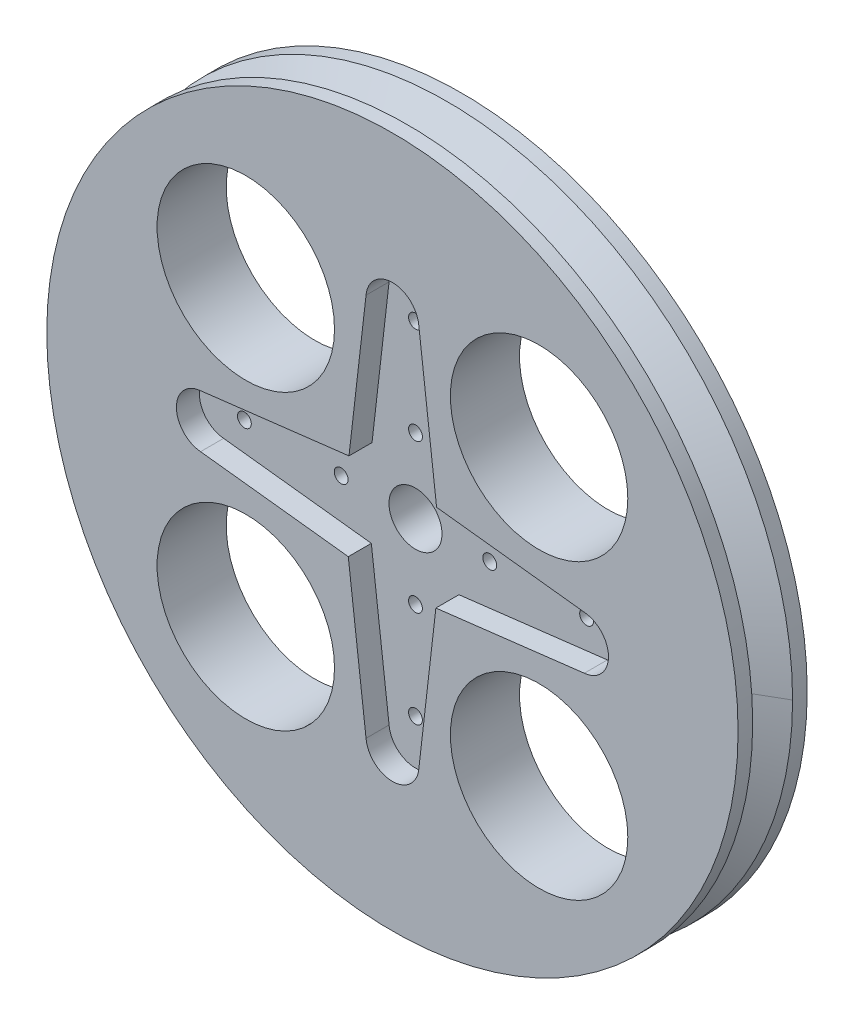
SolidWorks part; units mm, degrees
material "ABS"
ref_plane "Front Plane" through (0, 0, 0) normal (0, 0, 1) x (1, 0, 0)
ref_plane "Top Plane" through (0, 0, 0) normal (0, 1, 0) x (1, 0, 0)
ref_plane "Right Plane" through (0, 0, 0) normal (1, 0, 0) x (0, 0, -1)
sketch "Sketch1" plane through (0, 0, 0) normal (0, 0, 1) x (1, 0, 0)
  line L0 (-16.85, 0) -> (14.45, 0) construction
  line L1 (0, -6.45) -> (0, 6.45) construction
  line L2 (0, 0) -> (-21.2132, 21.2132) construction
  circle A0 centre (0, 0) radius 30
  circle A1 centre (-12.7279, 12.7279) radius 7.7
  circle A2 centre (12.7279, 12.7279) radius 7.7
  circle A3 centre (12.7279, -12.7279) radius 7.7
  circle A4 centre (-12.7279, -12.7279) radius 7.7
  circle A5 centre (0, 0) radius 2.3 construction
  circle A6 centre (0, 0) radius 2.3
  circle A7 centre (-14.85, 0) radius 0.6 construction
  circle A8 centre (-14.85, 0) radius 0.6
  circle A10 centre (6.45, 0) radius 0.6 construction
  circle A11 centre (6.45, 0) radius 0.6
  circle A12 centre (0, -6.45) radius 0.6
  circle A13 centre (-6.45, 0) radius 0.6
  circle A14 centre (0, 6.45) radius 0.6
  circle A15 centre (0, 14.85) radius 0.6
  circle A16 centre (14.85, 0) radius 0.6
  circle A17 centre (0, -14.85) radius 0.6
  point P23 (0, 0)
  point P38 (0, 0)
  point P45 (0, 0)
  dimension "D1" = 60
  dimension "D3" = 18
  dimension "D4" = 15.4
  dimension "D2" = 45
  dimension "D5" = 4
  dimension "D6" = 4
  dimension "D7" = 4
extrude "Boss-Extrude1" add sketch "Sketch1" against normal blind 6
sketch "Sketch2" plane through (0, 0, 0) normal (0, 1, 0) x (1, 0, 0)
  line L0 (-31.1569, 0.6) -> (-27, 3)
  line L1 (-27, 3) -> (-31.1569, 5.4)
  line L2 (-31.1569, 5.4) -> (-31.1569, 0.6)
  point P6 (-27.6339, 3.1141)
  dimension "D1" = 60
  dimension "D2" = 60
  dimension "D3" = 4.8
  dimension "D4" = 27
  dimension "D5" = 3
sweep "Cut-Sweep1" cut profiles "Sketch2" path edge at (30, 0, -6)
sketch "Sketch4" plane through (0, 0, 0) normal (0, 0, 1) x (1, 0, 0)
  line L0 (-3.7707, 3.8319) -> (-16.6527, 2.291)
  line L1 (-16.6527, -2.291) -> (-3.8319, -3.7707)
  line L2 (-2.291, 16.6527) -> (-3.7707, 3.8319)
  line L3 (3.8319, 3.7707) -> (2.291, 16.6527)
  line L4 (16.6527, 2.291) -> (3.8319, 3.7707)
  line L5 (3.7707, -3.8319) -> (16.6527, -2.291)
  line L6 (2.291, -16.6527) -> (3.7707, -3.8319)
  line L7 (-3.8319, -3.7707) -> (-2.291, -16.6527)
  arc A0 (-16.6527, 2.291) -> (-16.6527, -2.291) centre (-16.45, 0) ccw
  arc A1 (2.291, 16.6527) -> (-2.291, 16.6527) centre (0, 16.45) ccw
  arc A2 (16.6527, -2.291) -> (16.6527, 2.291) centre (16.45, 0) ccw
  arc A3 (-2.291, -16.6527) -> (2.291, -16.6527) centre (0, -16.45) ccw
  point P1 (0, 0)
  point P3 (0, 0)
  point P4 (0, 0)
  point P11 (0, 0)
  point P12 (-3.7707, -3.8319)
  point P23 (0, 0)
  point P25 (-3.4586, -3.4586)
  point P26 (-3.283, -3.6257)
  dimension "D1" = 4
extrude "Cut-Extrude1" cut sketch "Sketch4" against normal blind 2
